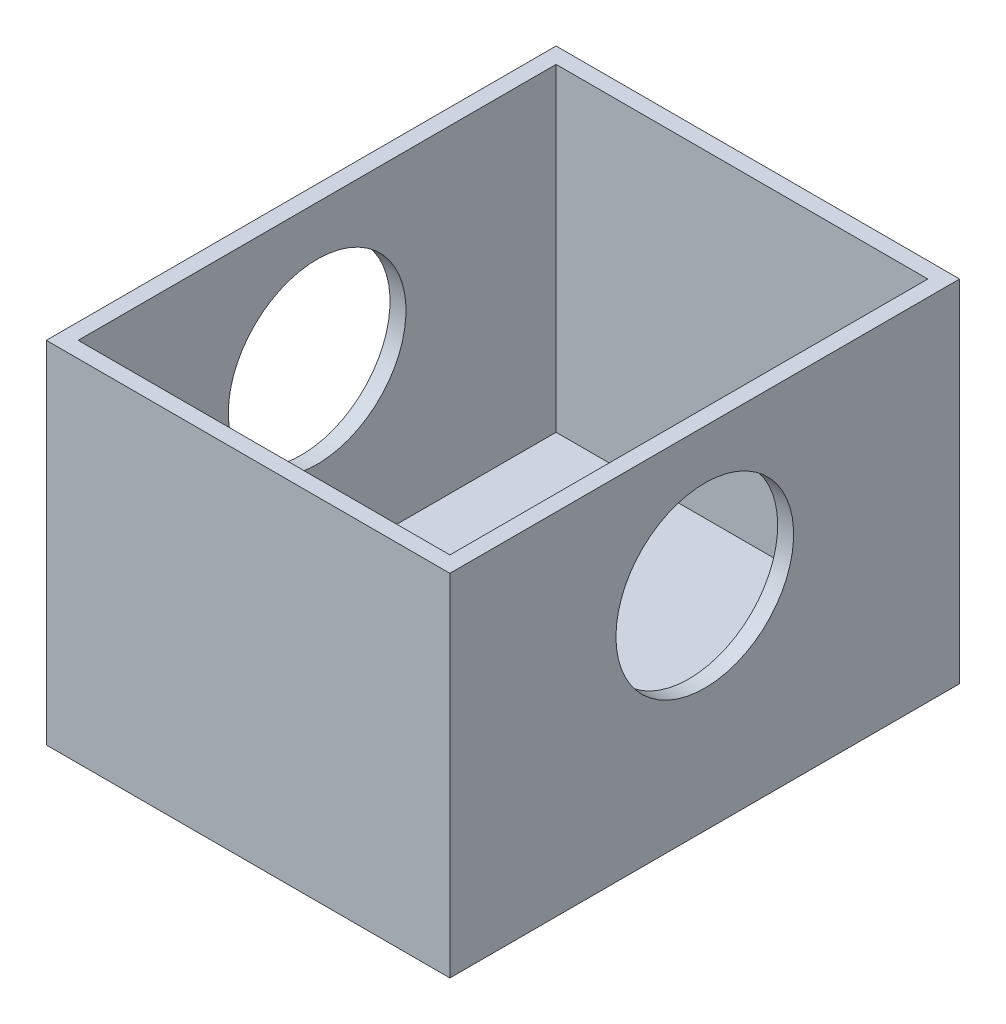
SolidWorks part; units mm, degrees
ref_plane "Front Plane" through (0, 0, 0) normal (0, 0, 1) x (1, 0, 0)
ref_plane "Top Plane" through (0, 0, 0) normal (0, 1, 0) x (1, 0, 0)
ref_plane "Right Plane" through (0, 0, 0) normal (1, 0, 0) x (0, 0, -1)
sketch "Sketch1" plane through (0, 0, 0) normal (0, 1, 0) x (1, 0, 0)
  line L0 (-7.9678, 7.5757) -> (-7.9678, -4.6163)
  line L1 (-7.9678, -4.6163) -> (1.6842, -4.6163)
  line L2 (1.6842, -4.6163) -> (1.6842, 7.5757)
  line L3 (1.6842, 7.5757) -> (-7.9678, 7.5757)
  dimension "D1" = 12.192
  dimension "D2" = 9.652
extrude "Boss-Extrude1" add sketch "Sketch1" along normal blind 8.382
sketch "Sketch4" plane through (0, 8.382, 0) normal (0, 1, 0) x (1, 0, 0)
  line L0 (1.3032, -4.2353) -> (1.3032, 7.1947)
  line L1 (1.3032, 7.1947) -> (-7.5868, 7.1947)
  line L2 (-7.5868, 7.1947) -> (-7.5868, -4.2353)
  line L3 (-7.5868, -4.2353) -> (1.3032, -4.2353)
  line L5 (-7.9678, 7.5757) -> (-7.9678, -4.6163) construction
  line L7 (1.6842, 7.5757) -> (-7.9678, 7.5757) construction
  dimension "D1" = 8.89
  dimension "D2" = 0.381
  dimension "D3" = 11.43
  dimension "D4" = 0.381
extrude "Cut-Extrude1" cut sketch "Sketch4" against normal blind 7.62
sketch "Sketch6" plane through (-7.9678, 0, 0) normal (-1, 0, 0) x (0, 0, 1)
  line L0 (-7.5757, 8.382) -> (-7.5757, 0) construction
  line L1 (-7.5757, 0) -> (4.6163, 0) construction
  circle A0 centre (-1.4797, 5.08) radius 2.1247
  point P2 (0, 0)
  point P5 (0, 0)
  dimension "D2" = 4.2494
  dimension "D1" = 5.08
  dimension "D3" = 6.096
extrude "Cut-Extrude2" cut sketch "Sketch6" against normal through all
ref_plane "Plane1" through (0, 0, -1.4797) normal (0, 0, 1) x (1, 0, 0)
ref_plane "Plane2" through (-3.1418, 0, 0) normal (1, 0, 0) x (0, 0, -1)
